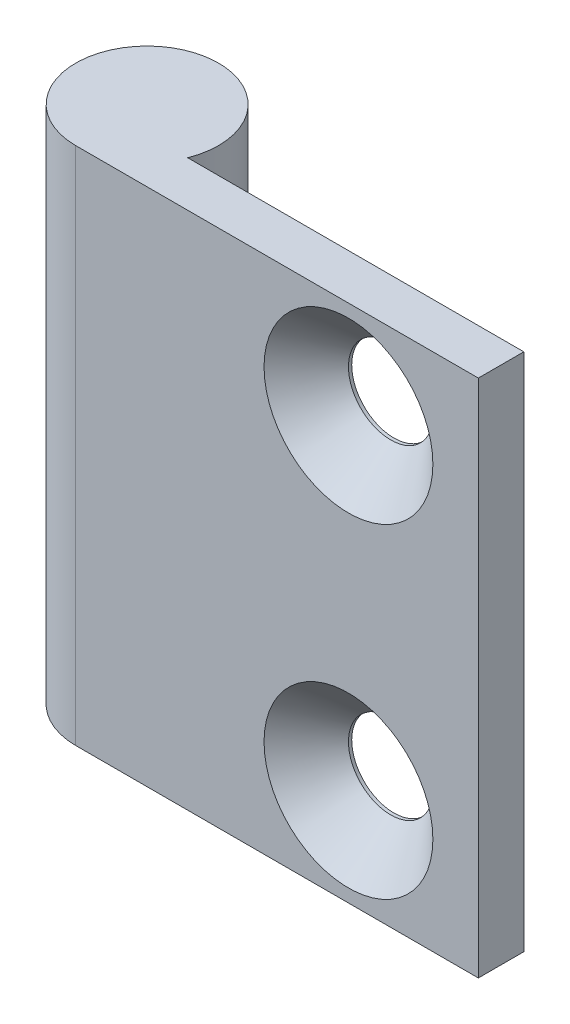
SolidWorks part; units mm, degrees
ref_plane "Piano frontale" through (0, 0, 0) normal (0, 0, 1) x (1, 0, 0)
ref_plane "Piano superiore" through (0, 0, 0) normal (0, 1, 0) x (1, 0, 0)
ref_plane "Piano destro" through (0, 0, 0) normal (1, 0, 0) x (0, 0, -1)
ref_plane "Plane1" through (0, -41.7, 0) normal (0, -1, 0) x (1, 0, 0)
sketch "Sketch1" plane through (0, -41.7, 0) normal (0, -1, 0) x (1, 0, 0)
  line L0 (31, 5.5) -> (0, 5.5)
  line L1 (5.1235, 2) -> (31, 2)
  line L2 (31, 2) -> (31, 5.5)
  arc A0 (0, 5.5) -> (5.1235, 2) centre (0, 0) ccw
extrude "Extrude1" add sketch "Sketch1" against normal blind 40
hole_wizard "HoleWzd1" positions "Sketch5" profile "Sketch4" countersink size "M6" standard "Ansi Metric"
sketch "Sketch5" plane through (0, 0, 5.5) normal (0, 0, 1) x (1, 0, 0)
  point P0 (21, -34.2)
  point P1 (21, -9.2)
sketch "Sketch4" plane through (21, -34.2, 5.5) normal (1, 0, 0) x (0, -1, 0)
  line L0 (0, 0) -> (0, 11)
  line L1 (0, 11) -> (3.25, 11)
  line L2 (3.25, 11) -> (3.25, 3.25)
  line L3 (3.25, 3.25) -> (6.5, 0)
  line L5 (6.5, 0) -> (0, 0)
  line L6 (-3.25, 3.25) -> (-6.5, 0) construction
  line L11 (0, -6.35) -> (0, 107.95) construction
  dimension "Thru Hole Dia." = 6.5
  dimension "Thru Hole Depth" = 11
  dimension "Near C'Sink Dia." = 13
  dimension "Near C'Sink Angle" = 90
